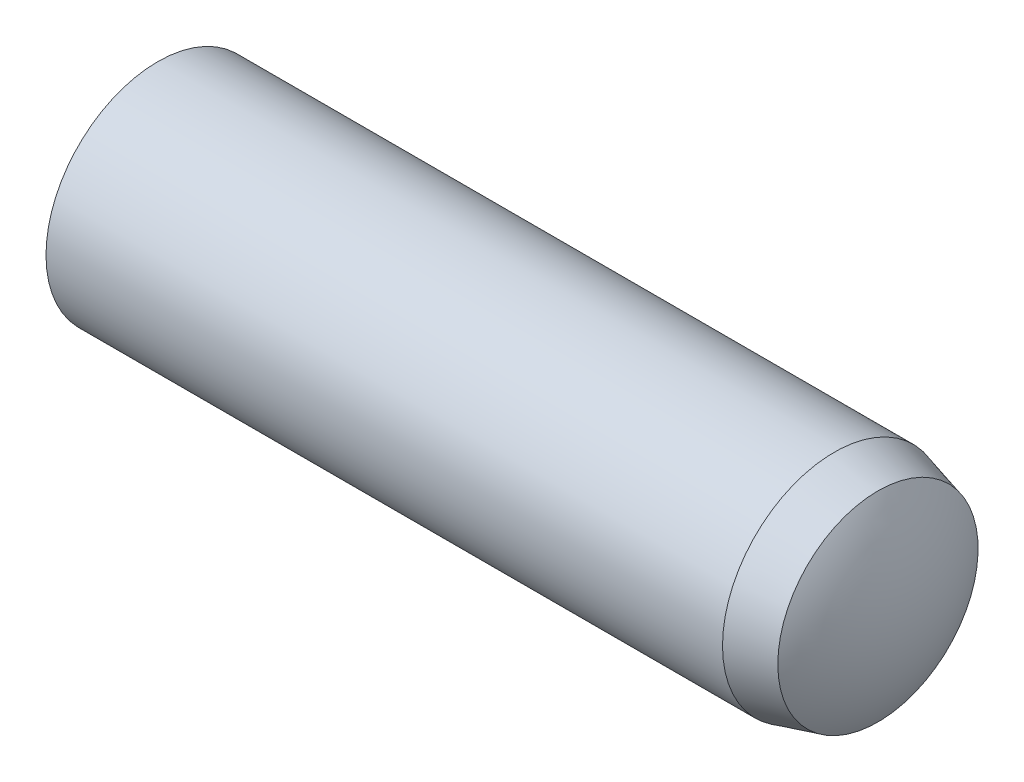
SolidWorks part; units mm, degrees
ref_plane "Front Plane" through (0, 0, 0) normal (0, 0, 1) x (1, 0, 0)
ref_plane "Top Plane" through (0, 0, 0) normal (0, 1, 0) x (1, 0, 0)
ref_plane "Right Plane" through (0, 0, 0) normal (1, 0, 0) x (0, 0, -1)
sketch "Sketch1" plane through (0, 0, 0) normal (0, 0, 1) x (1, 0, 0)
  line L0 (-14, 0) -> (14, 0) construction
  line L1 (14, 4) -> (14, -4) construction
  line L2 (-14, 4) -> (-14, -4) construction
  line L3 (11.4, 4) -> (11.4, -4) construction
  line L4 (-12.8, 4) -> (-12.8, -4) construction
  line L5 (-14, 0) -> (-12.8, 0) construction
  line L6 (14, 0) -> (11.4, 0) construction
  line L7 (12.96, 4) -> (12.96, -4) construction
  dimension "D1" = 2.6
  dimension "Dia" = 8
  dimension "D2" = 1.2
  dimension "Length" = 28
  dimension "D3" = 1.56
sketch "Sketch2" plane through (0, 0, 0) normal (1, 0, 0) x (0, 0, -1)
  circle A0 centre (0, 0) radius 4
extrude "Extrude1" add sketch "Sketch2" against normal up to vertex (14 mm away) and the other way up to vertex (14 mm away) up to point (-14, 0, 0) other way up to point (14, 0, 0)
sketch "Sketch5" plane through (0, 0, 0) normal (0, 0, 1) x (1, 0, 0)
  line L0 (11.4, 4) -> (11.4, 4.5)
  line L1 (11.4, 4.5) -> (14.5, 4.5)
  line L2 (14.5, 4.5) -> (14.5, 0)
  line L3 (14, 0) -> (14.5, 0)
  line L5 (-12.8, 4) -> (-12.8, 4.5)
  line L6 (-12.8, 4.5) -> (-14.5, 4.5)
  line L7 (-14.5, 4.5) -> (-14.5, 0)
  line L8 (11.4, 4) -> (12.96, 3.582)
  line L10 (-14, 0) -> (-14.5, 0)
  line L11 (-14, 4) -> (-14, -4) construction
  line L13 (11.4, 4) -> (11.4, -4) construction
  line L15 (-14, 0) -> (14, 0) construction
  line L16 (12.96, 4) -> (12.96, -4) construction
  line L17 (14, 4) -> (14, -4) construction
  arc A0 (12.96, 3.582) -> (14, 0) centre (7.3114, 0) cw
  arc A1 (-12.8, 4) -> (-14, 0) centre (-6.7333, 0) ccw
  dimension "D1" = 15
  dimension "D2" = 0.5
revolve "Cut-Revolve1" cut sketch "Sketch5" angle 360 about L0
equation "\"D1@Sketch1\" = \"Dia@Sketch1\"*.325"
equation "\"D2@Sketch1\" = \"Dia@Sketch1\"*.15"
equation "\"D3@Sketch1\" = \"D1@Sketch1\"*.6"
